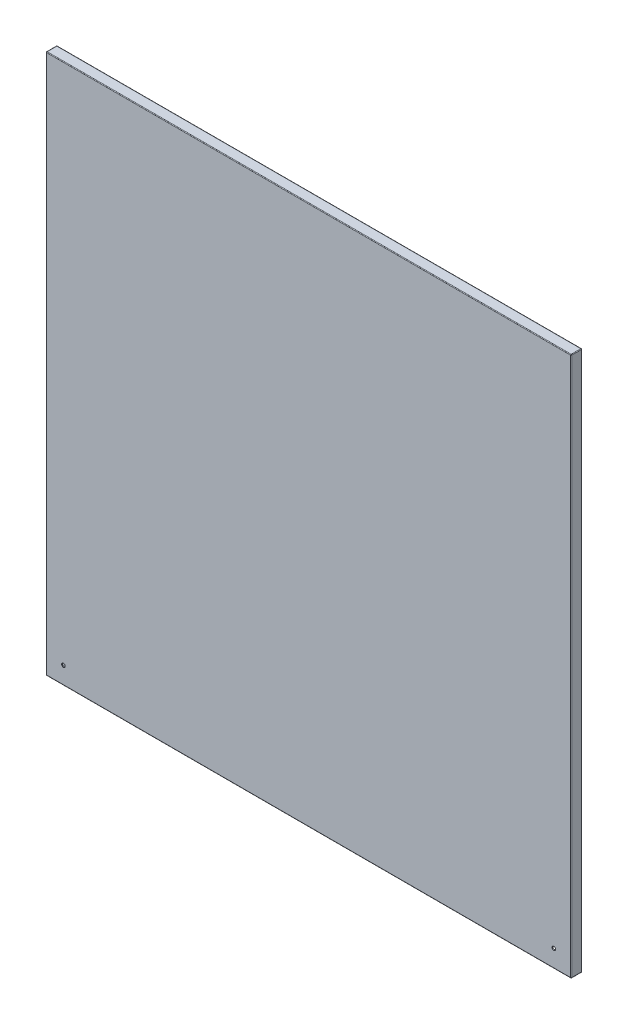
SolidWorks part; units mm, degrees
ref_plane "前视基准面" through (0, 0, 0) normal (0, 0, 1) x (1, 0, 0)
ref_plane "上视基准面" through (0, 0, 0) normal (0, 1, 0) x (1, 0, 0)
ref_plane "右视基准面" through (0, 0, 0) normal (1, 0, 0) x (0, 0, -1)
sketch "草图1" plane through (0, 0, 0) normal (0, 0, 1) x (1, 0, 0)
  line L1 (437.5, -450) -> (-437.5, -450)
  line L2 (437.5, -450) -> (437.5, 450)
  line L3 (437.5, 450) -> (-437.5, 450)
  line L4 (-437.5, -450) -> (-437.5, 450)
  line L5 (437.5, -450) -> (-437.5, 450) construction
  line L6 (437.5, 450) -> (-437.5, -450) construction
  point P0 (0, 0)
  dimension "D1" = 875
  dimension "D2" = 900
extrude "凸台-拉伸1" add sketch "草图1" along normal blind 1.5
sketch "草图2" plane through (0, 0, 0) normal (0, 0, -1) x (-1, 0, 0)
  line L1 (-437.5, -450) -> (437.5, -450)
  line L2 (-437.5, -450) -> (-437.5, 450)
  line L3 (-437.5, 450) -> (437.5, 450)
  line L4 (437.5, -450) -> (437.5, 450)
  line L5 (-437.5, -450) -> (437.5, 450) construction
  line L6 (-437.5, 450) -> (437.5, -450) construction
  line L7 (-436, -448.5) -> (436, -448.5)
  line L8 (-436, -448.5) -> (-436, 448.5)
  line L9 (-436, 448.5) -> (436, 448.5)
  line L10 (436, -448.5) -> (436, 448.5)
  line L11 (-436, -448.5) -> (436, 448.5) construction
  line L12 (-436, 448.5) -> (436, -448.5) construction
  point P0 (0, 0)
  point P7 (0, 0)
  dimension "D1" = 1.5
  dimension "D2" = 1.5
extrude "凸台-拉伸2" add sketch "草图2" along normal blind 15
sketch "草图3" plane through (0, 0, -15) normal (0, 0, -1) x (-1, 0, 0)
  line L1 (-437.5, -450) -> (437.5, -450)
  line L2 (-437.5, -450) -> (-437.5, 450)
  line L3 (-437.5, 450) -> (437.5, 450)
  line L4 (437.5, -450) -> (437.5, 450)
  line L5 (-437.5, -450) -> (437.5, 450) construction
  line L6 (-437.5, 450) -> (437.5, -450) construction
  line L7 (-422.5, -440) -> (422.5, -440)
  line L8 (-422.5, -440) -> (-422.5, 440)
  line L9 (-422.5, 440) -> (422.5, 440)
  line L10 (422.5, -440) -> (422.5, 440)
  line L11 (-422.5, -440) -> (422.5, 440) construction
  line L12 (-422.5, 440) -> (422.5, -440) construction
  point P0 (0, 0)
  point P7 (0, 0)
  dimension "D1" = 10
  dimension "D2" = 15
extrude "凸台-拉伸3" add sketch "草图3" along normal blind 1.5
sketch "草图6" plane through (0, 0, 1.5) normal (0, 0, 1) x (1, 0, 0)
  line L0 (0, -450) -> (0, 450) construction
  line L1 (-437.5, -450) -> (437.5, -450) construction
  line L2 (437.5, 450) -> (-437.5, 450) construction
  line L3 (-437.5, 450) -> (-437.5, -450) construction
  circle A0 centre (-408.5, -421) radius 3
  circle A1 centre (408.5, -421) radius 3
  dimension "D3" = 6
  dimension "D1" = 29
  dimension "D2" = 29
extrude "切除-拉伸1" cut sketch "草图6" against normal through all
fillet "圆角1" radius 1 12 edges at (0, -450, -16.5) (437.5, 0, -16.5) (0, 450, -16.5) (-437.5, 450, -7.5) (-437.5, 0, -16.5) (437.5, -450, -7.5) (-437.5, -450, -7.5) (-437.5, 0, 1.5) (0, -450, 1.5) (0, 450, 1.5) (437.5, 0, 1.5) (437.5, 450, -7.5)
